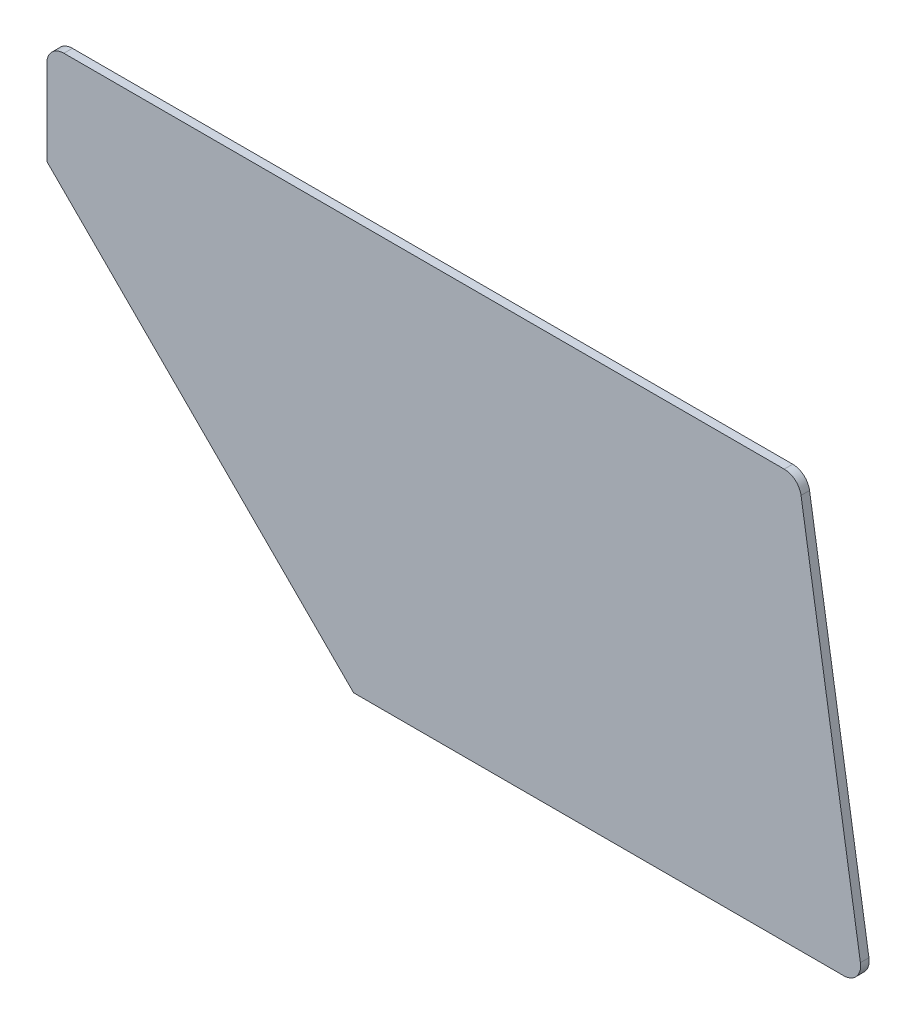
SolidWorks part; units mm, degrees
material "6061-T6 (SS)"
ref_plane "Front Plane" through (0, 0, 0) normal (0, 0, 1) x (1, 0, 0)
ref_plane "Top Plane" through (0, 0, 0) normal (0, 1, 0) x (1, 0, 0)
ref_plane "Right Plane" through (0, 0, 0) normal (1, 0, 0) x (0, 0, -1)
sketch "Sketch1" plane through (0, 0, 0) normal (0, 0, 1) x (1, 0, 0)
  line L0 (0, -6.35) -> (0, -38.1)
  line L1 (0, -38.1) -> (114.3, -152.4)
  line L2 (114.3, -152.4) -> (296.8625, -152.4)
  line L3 (303.1343, -145.0566) -> (281.008, -5.3566)
  line L4 (274.7362, 0) -> (6.35, 0)
  arc A0 (296.8625, -152.4) -> (303.1343, -145.0566) centre (296.8625, -146.05) ccw
  arc A1 (274.7362, 0) -> (281.008, -5.3566) centre (274.7362, -6.35) cw
  arc A2 (6.35, 0) -> (0, -6.35) centre (6.35, -6.35) ccw
  dimension "D1" = 6.35
  dimension "D2" = 6.35
  dimension "D3" = 6.35
  dimension "D4" = 152.4
  dimension "D5" = 303.2125
  dimension "D6" = 81
  dimension "D7" = 45
  dimension "D8" = 38.1
extrude "Boss-Extrude1" add sketch "Sketch1" along normal blind 3.175
